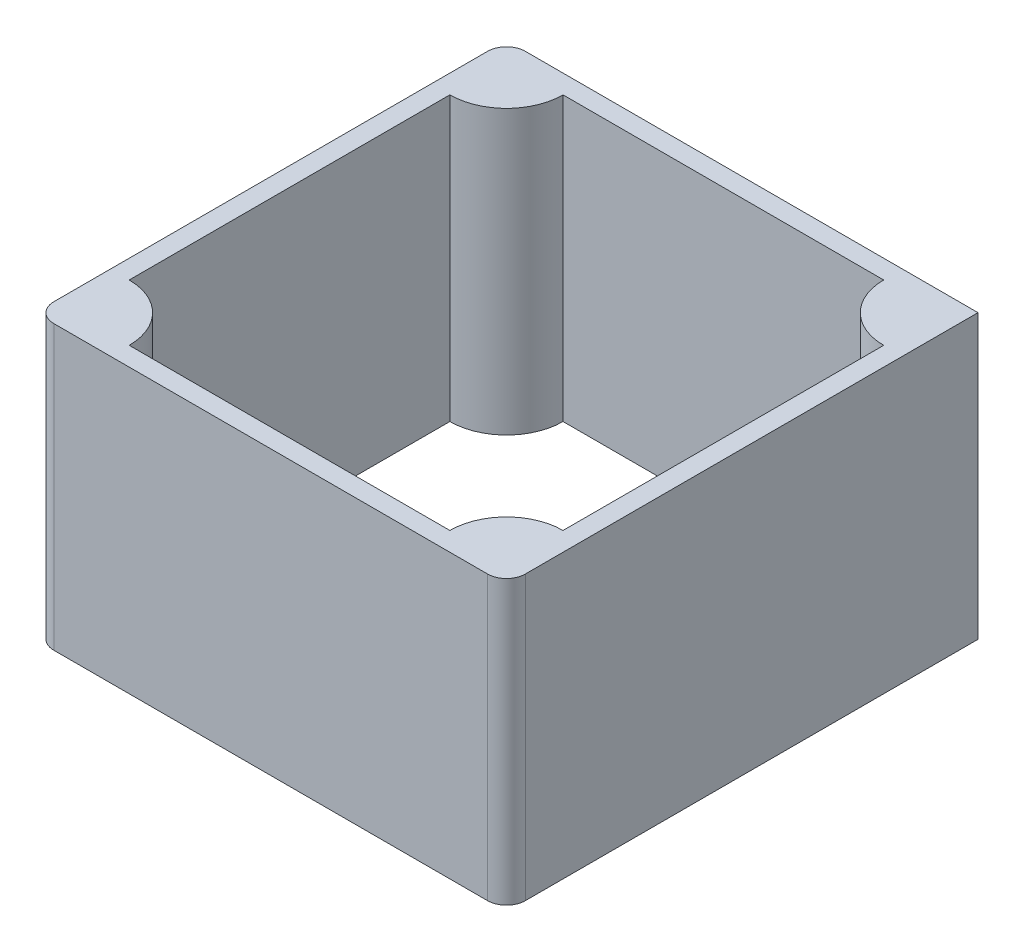
SolidWorks part; units mm, degrees
ref_plane "Plan de face" through (0, 0, 0) normal (0, 0, 1) x (1, 0, 0)
ref_plane "Plan de dessus" through (0, 0, 0) normal (0, 1, 0) x (1, 0, 0)
ref_plane "Plan de droite" through (0, 0, 0) normal (1, 0, 0) x (0, 0, -1)
sketch "Esquisse1" plane through (0, 0, 0) normal (0, 1, 0) x (1, 0, 0)
  line L1 (-11.2955, 9.6623) -> (38.7045, 9.6623)
  line L2 (-11.2955, 9.6623) -> (-11.2955, -40.3377)
  line L3 (-11.2955, -40.3377) -> (38.7045, -40.3377)
  line L4 (38.7045, 9.6623) -> (38.7045, -40.3377)
  line L5 (13.7045, 9.6623) -> (13.7045, 7.6623) construction
  line L7 (-3.2955, 7.6623) -> (30.7045, 7.6623)
  line L8 (-9.2955, 1.6623) -> (-9.2955, -32.3377)
  line L9 (-3.2955, -38.3377) -> (30.7045, -38.3377)
  line L10 (36.7045, 1.6623) -> (36.7045, -32.3377)
  line L22 (-3.2955, -40.3377) -> (-3.2955, -53.574) construction
  arc A0 (-9.2955, 1.6623) -> (-3.2955, 7.6623) centre (-9.2955, 7.6623) ccw
  arc A1 (-3.2955, -38.3377) -> (-9.2955, -32.3377) centre (-9.2955, -38.3377) ccw
  arc A2 (30.7045, 7.6623) -> (36.7045, 1.6623) centre (36.7045, 7.6623) ccw
  arc A3 (36.7045, -32.3377) -> (30.7045, -38.3377) centre (36.7045, -38.3377) ccw
  point P8 (13.7045, -15.3377)
  point P16 (13.7045, 15.837)
  point P23 (45.9636, -15.3377)
  dimension "D1" = 50
  dimension "D2" = 50
  dimension "D3" = 46
  dimension "D4" = 46
extrude "Boss.-Extru.1" add sketch "Esquisse1" along normal blind 30
fillet "Congé1" radius 2 3 edges at (-11.2955, 15, -9.6623) (38.7045, 15, 40.3377) (-11.2955, 15, 40.3377)
